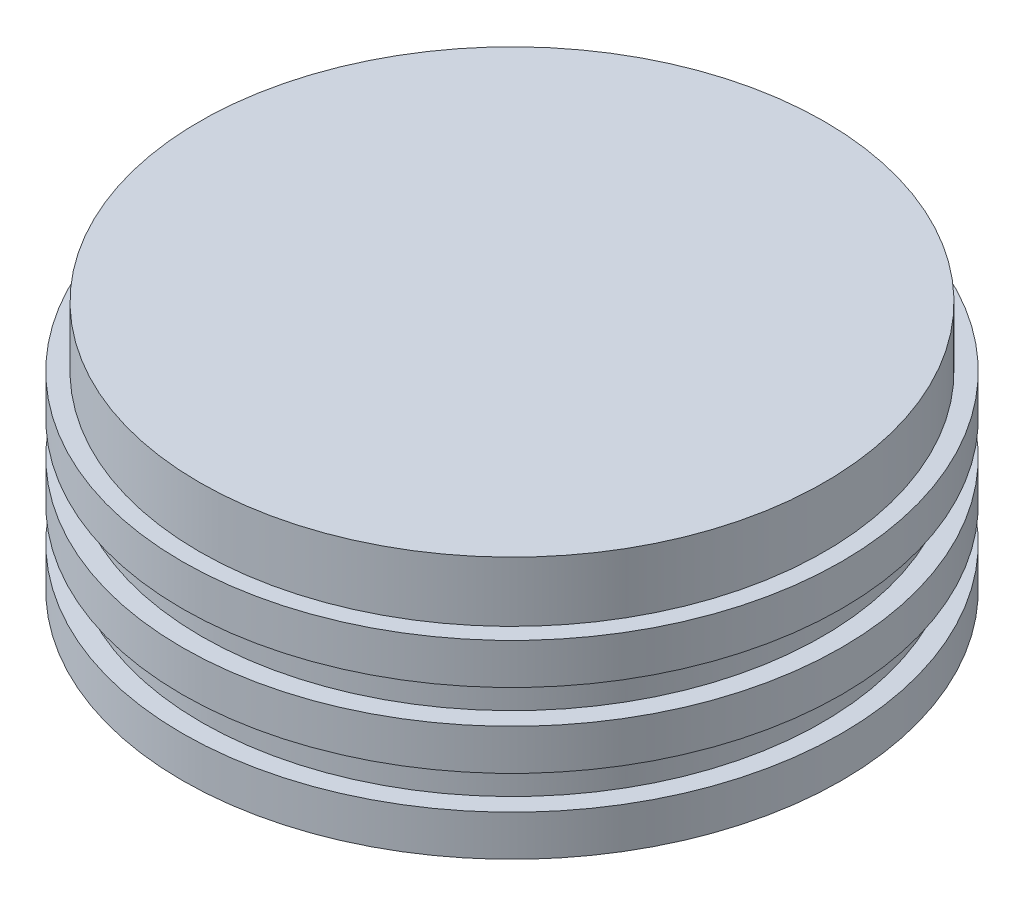
SolidWorks part; units mm, degrees
material "6061-T6 (SS)"
ref_plane "Front Plane" through (0, 0, 0) normal (0, 0, 1) x (1, 0, 0)
ref_plane "Top Plane" through (0, 0, 0) normal (0, 1, 0) x (1, 0, 0)
ref_plane "Right Plane" through (0, 0, 0) normal (1, 0, 0) x (0, 0, -1)
sketch "Sketch8" plane through (0, 0, 0) normal (0, 0, 1) x (1, 0, 0)
  line L0 (0, 0) -> (0, 26.416)
  line L1 (0, 26.416) -> (-33.0835, 26.416)
  line L2 (-33.0835, 26.416) -> (-33.0835, 20.066)
  line L3 (-33.0835, 20.066) -> (-34.8996, 20.066)
  line L4 (-34.8996, 20.066) -> (-34.8996, 15.748)
  line L5 (-34.8996, 15.748) -> (-32.8676, 15.748)
  line L7 (-32.8676, 7.874) -> (-34.8996, 7.874)
  line L8 (-34.8996, 7.874) -> (-34.8996, 12.192)
  line L11 (-32.8676, 4.318) -> (-34.8996, 4.318)
  line L12 (-34.8996, 4.318) -> (-34.8996, 0)
  line L13 (-34.8996, 0) -> (0, 0)
  line L14 (-34.8996, 12.192) -> (-32.8676, 12.192)
  line L15 (-32.8676, 15.748) -> (-32.8676, 12.192)
  line L16 (-32.8676, 7.874) -> (-32.8676, 4.318)
  dimension "D1" = 6.35
  dimension "D2" = 34.8996
  dimension "D3" = 32.8676
  dimension "D4" = 3.556
  dimension "D5" = 3.556
  dimension "D6" = 4.318
  dimension "D7" = 4.318
  dimension "D8" = 4.318
  dimension "D9" = 33.0835
revolve "Revolve1" add sketch "Sketch8" angle 360 about L0
hole_wizard "Tap Drill for 3/8-16 Tap1" positions "Sketch9" profile "Sketch11" hole size "3/8-16" standard "ANSI Inch"
sketch "Sketch9" plane through (0, 0, 0) normal (0, -1, 0) x (-1, 0, 0)
  point P0 (0, 0)
sketch "Sketch11" plane through (0, 0, 0) normal (1, 0, 0) x (0, 0, -1)
  line L0 (0, 0) -> (0, 18.2597)
  line L1 (0, 18.2597) -> (3.9687, 15.875)
  line L2 (3.9687, 15.875) -> (3.9687, 0)
  line L5 (3.9687, 0) -> (0, 0)
  line L10 (0, 18.2597) -> (-3.9688, 15.875) construction
  line L11 (0, -6.35) -> (0, 107.95) construction
  dimension "Hole Dia." = 7.9375
  dimension "Hole Depth" = 15.875
  dimension "Drill Angle" = 118
